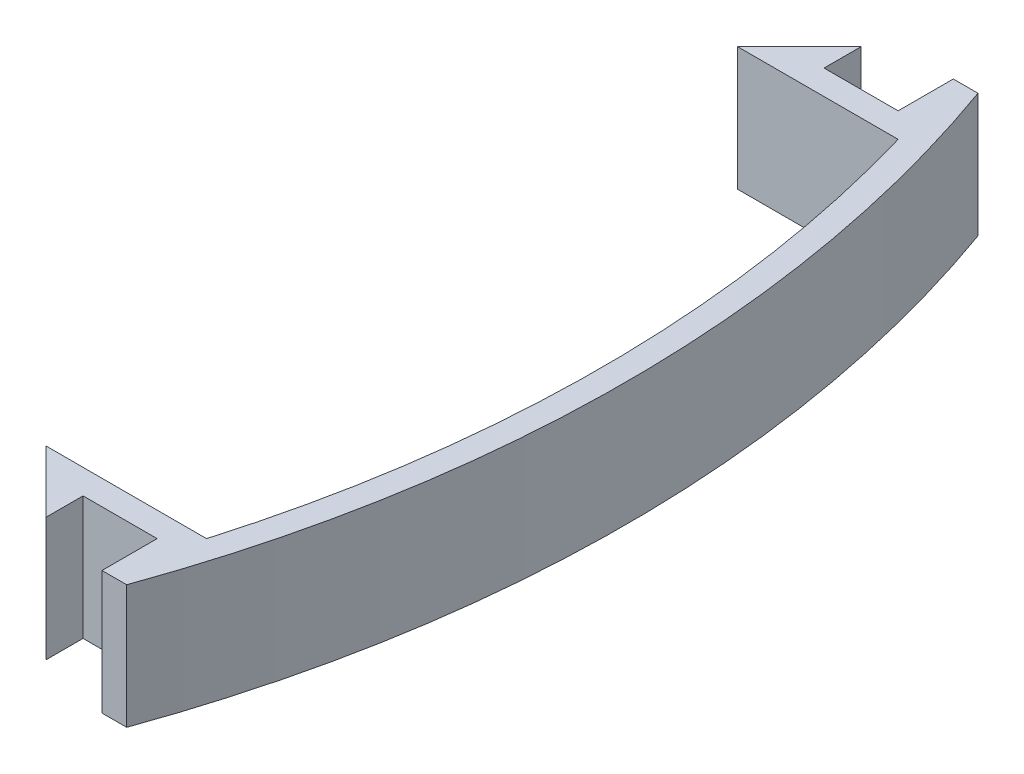
SolidWorks part; units mm, degrees
ref_plane "Plan de face" through (0, 0, 0) normal (0, 0, 1) x (1, 0, 0)
ref_plane "Plan de dessus" through (0, 0, 0) normal (0, 1, 0) x (1, 0, 0)
ref_plane "Plan de droite" through (0, 0, 0) normal (1, 0, 0) x (0, 0, -1)
sketch "Esquisse1" plane through (0, 0, 0) normal (0, 1, 0) x (1, 0, 0)
  line L0 (0, 73.119) -> (0, -80.3873) construction
  line L1 (0, -28) -> (-13, -28)
  line L2 (-13, -28) -> (-8, -33)
  line L3 (-8, -33) -> (-8, -30)
  line L4 (-8, -30) -> (-2, -30)
  line L5 (-2, -30) -> (-2, -34.4674)
  line L6 (0, -34.4674) -> (-2, -34.4674)
  line L7 (0, 34.4674) -> (-2, 34.4674)
  line L13 (0, 28) -> (-13, 28)
  line L14 (-13, 28) -> (-8, 33)
  line L15 (-8, 33) -> (-8, 30)
  line L16 (-8, 30) -> (-2, 30)
  line L17 (-2, 30) -> (-2, 34.4674)
  arc A0 (0, 28) -> (0, -28) centre (-96, 0) cw
  arc A1 (0, -34.4674) -> (0, 34.4674) centre (-96, 0) ccw
  dimension "D9" = 2
  dimension "D10" = 100
  dimension "D1" = 28
  dimension "D2" = 56
  dimension "D3" = 2
  dimension "D4" = 3
  dimension "D5" = 13
  dimension "D6" = 6
  dimension "D7" = 5
  dimension "D17" = 13
  dimension "D18" = 6
  dimension "D19" = 3
  dimension "D21" = 5
  dimension "D22" = 2
extrude "Boss.-Extru.1" add sketch "Esquisse1" along normal blind 10
